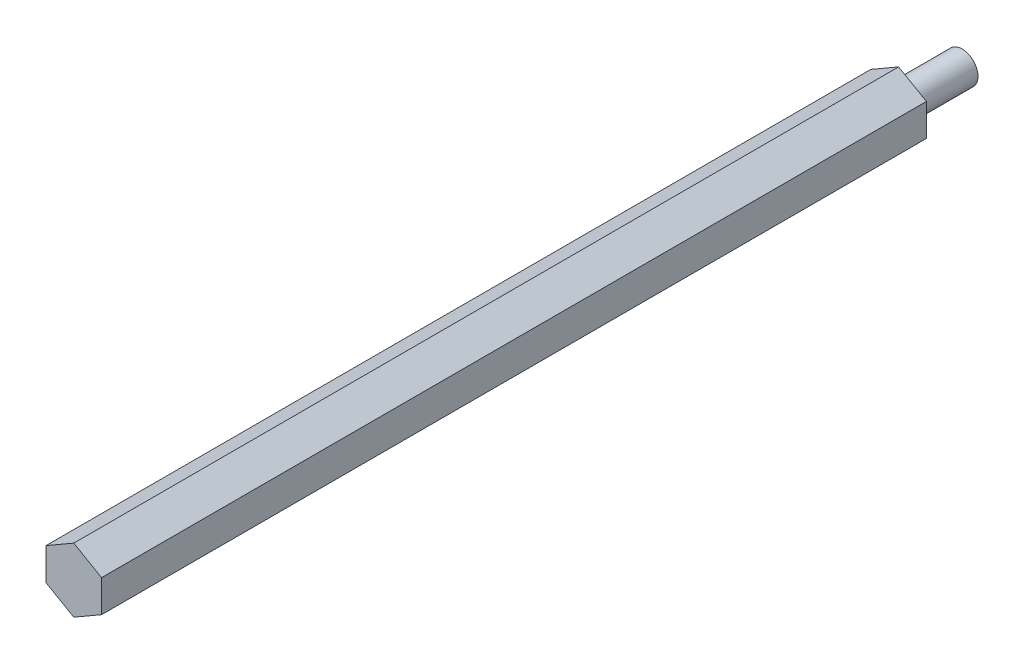
SolidWorks part; units mm, degrees
ref_plane "Front Plane" through (0, 0, 0) normal (0, 0, 1) x (1, 0, 0)
ref_plane "Top Plane" through (0, 0, 0) normal (0, 1, 0) x (1, 0, 0)
ref_plane "Right Plane" through (0, 0, 0) normal (1, 0, 0) x (0, 0, -1)
sketch "Sketch1" plane through (0, 0, 0) normal (0, 0, 1) x (1, 0, 0)
  line L1 (0, 6.4158) -> (-5.5562, 3.2079) construction
  line L2 (-5.5562, 3.2079) -> (-5.5562, -3.2079) construction
  line L3 (-5.5562, -3.2079) -> (0, -6.4158) construction
  line L4 (0, -6.4158) -> (5.5562, -3.2079) construction
  line L5 (5.5562, -3.2079) -> (5.5562, 3.2079) construction
  line L6 (5.5562, 3.2079) -> (0, 6.4158) construction
  circle A2 centre (0, 0) radius 5.5562 construction
  dimension "Width" = 11.1125
sketch "Sketch2" plane through (0, 0, 0) normal (1, 0, 0) x (0, 0, -1)
  line L0 (-82.5, 6.4158) -> (82.5, 6.4158) construction
  point P2 (0, 6.4158)
  point P3 (54.7188, 6.4158)
  point P4 (-54.7188, 6.4158)
  dimension "D2" = 27.7812
  dimension "D1" = 27.7812
sketch "Sketch3" plane through (0, 0, 0) normal (0, 0, 1) x (1, 0, 0)
  line L0 (-5.5562, -3.2079) -> (0, -6.4158) construction
  line L1 (0, -6.4158) -> (5.5562, -3.2079) construction
  line L2 (5.5562, -3.2079) -> (5.5562, 3.2079) construction
  line L3 (5.5562, 3.2079) -> (0, 6.4158) construction
  line L4 (0, 6.4158) -> (-5.5562, 3.2079) construction
  line L5 (-5.5562, 3.2079) -> (-5.5562, -3.2079) construction
  line L6 (-5.5562, -3.2079) -> (0, -6.4158)
  line L7 (0, -6.4158) -> (5.5562, -3.2079)
  line L8 (5.5562, -3.2079) -> (5.5562, 3.2079)
  line L9 (5.5562, 3.2079) -> (0, 6.4158)
  line L10 (0, 6.4158) -> (-5.5562, 3.2079)
  line L11 (-5.5562, 3.2079) -> (-5.5562, -3.2079)
extrude "Boss-Extrude2" add sketch "Sketch3" along normal up to vertex (82.5 mm away) and the other way up to vertex (82.5 mm away) up to point (0, 6.4158, 82.5) other way up to point (0, 6.4158, -82.5)
sketch "Sketch4" plane through (0, 0, -82.5) normal (0, 0, 1) x (1, 0, 0)
  circle A0 centre (0, 0) radius 3.175
  dimension "D1" = 6.35
extrude "Boss-Extrude3" add sketch "Sketch4" against normal blind 12.7
equation "\"D2@Sketch2\" = \"D1@Sketch2\""
equation "\"D1@Sketch2\" = \"Width@Sketch1\" * 2.5"
